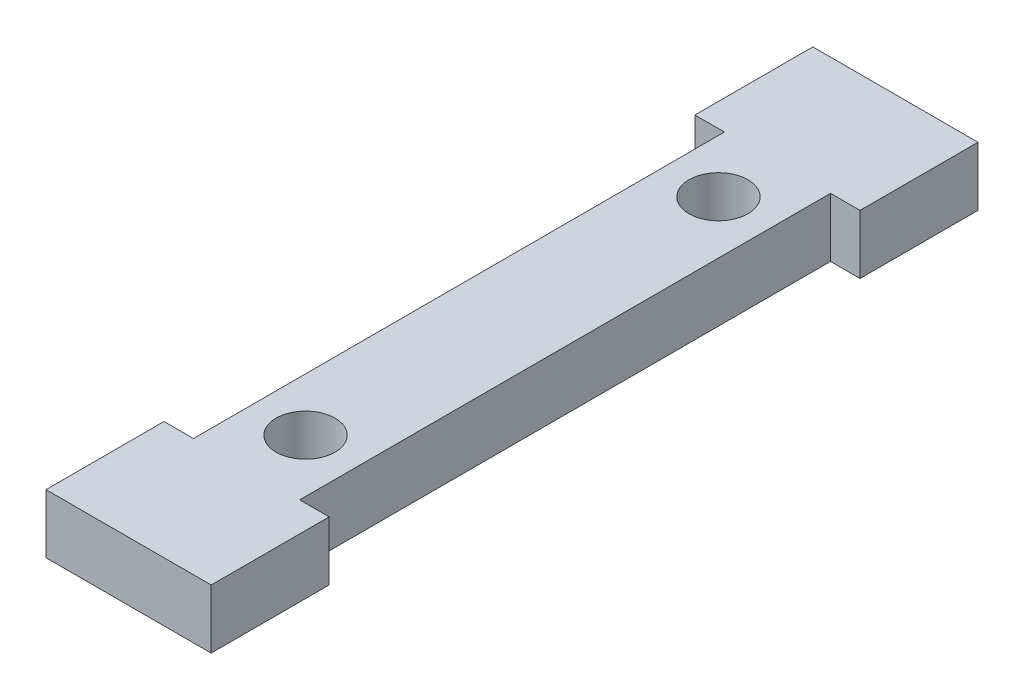
SolidWorks part; units mm, degrees
ref_plane "Front Plane" through (0, 0, 0) normal (0, 0, 1) x (1, 0, 0)
ref_plane "Top Plane" through (0, 0, 0) normal (0, 1, 0) x (1, 0, 0)
ref_plane "Right Plane" through (0, 0, 0) normal (1, 0, 0) x (0, 0, -1)
sketch "Sketch1" plane through (0, 0, 0) normal (0, 1, 0) x (1, 0, 0)
  line L0 (-3.175, 0) -> (14.605, 0)
  line L1 (14.605, 0) -> (14.605, 12.7)
  line L2 (14.605, 12.7) -> (11.43, 12.7)
  line L3 (11.43, 12.7) -> (11.43, 69.85)
  line L4 (11.43, 69.85) -> (14.605, 69.85)
  line L5 (14.605, 69.85) -> (14.605, 82.55)
  line L6 (14.605, 82.55) -> (-3.175, 82.55)
  line L7 (-3.175, 82.55) -> (-3.175, 69.85)
  line L8 (-3.175, 69.85) -> (0, 69.85)
  line L9 (0, 69.85) -> (0, 12.7)
  line L10 (0, 12.7) -> (-3.175, 12.7)
  line L11 (-3.175, 12.7) -> (-3.175, 0)
  line L12 (5.715, 82.55) -> (5.715, 0) construction
  circle A0 centre (5.715, 63.5) radius 3.175
  circle A1 centre (5.715, 19.05) radius 3.175
  point P20 (5.715, 41.275)
  dimension "D6" = 6.35
  dimension "D7" = 6.35
  dimension "D1" = 44.45
  dimension "D2" = 17.78
  dimension "D3" = 82.55
  dimension "D4" = 12.7
  dimension "D5" = 3.175
  dimension "D8" = 22.225
extrude "Boss-Extrude2" add sketch "Sketch1" along normal blind 6.35
